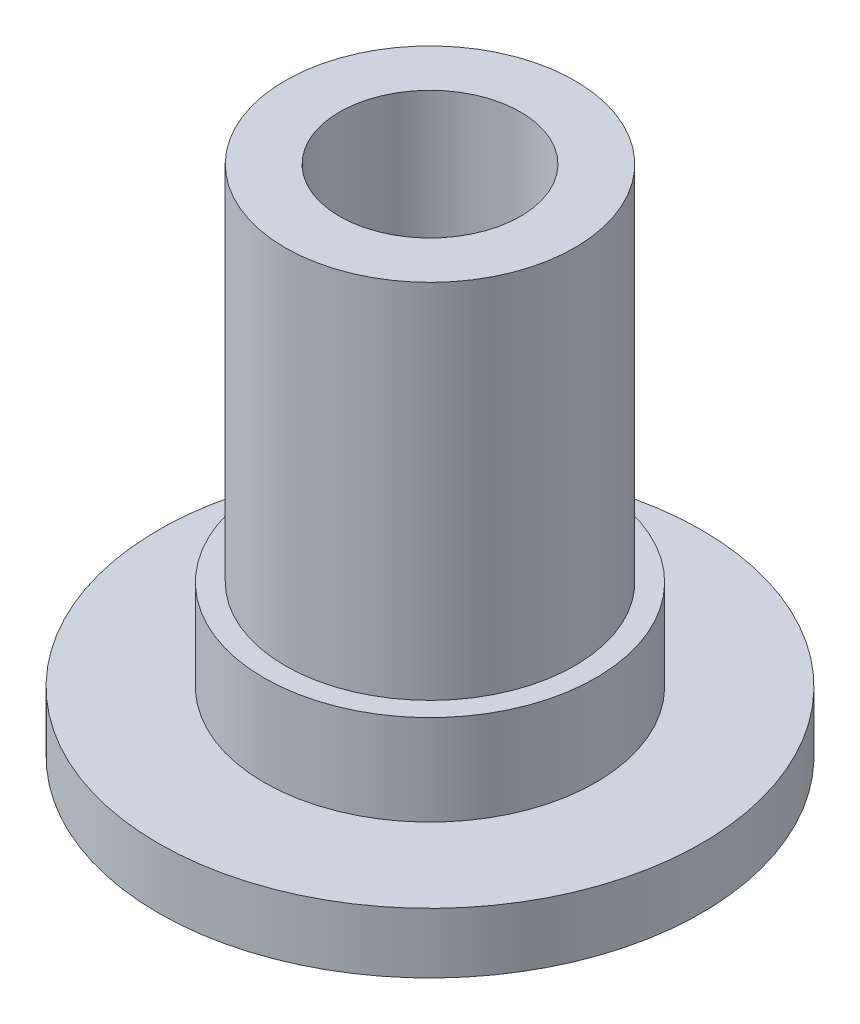
SolidWorks part; units mm, degrees
ref_plane "Спереди" through (0, 0, 0) normal (0, 0, 1) x (1, 0, 0)
ref_plane "Сверху" through (0, 0, 0) normal (0, 1, 0) x (1, 0, 0)
ref_plane "Справа" through (0, 0, 0) normal (1, 0, 0) x (0, 0, -1)
sketch "Эскиз1" plane through (0, 0, 0) normal (0, 1, 0) x (1, 0, 0)
  circle A0 centre (0, 0) radius 9
extrude "Бобышка-Вытянуть1" add sketch "Эскиз1" along normal blind 2
sketch "Эскиз2" plane through (0, 2, 0) normal (0, 1, 0) x (1, 0, 0)
  circle A0 centre (0, 0) radius 5.5
extrude "Бобышка-Вытянуть2" add sketch "Эскиз2" along normal blind 3
sketch "Эскиз5" plane through (0, 5, 0) normal (0, 1, 0) x (1, 0, 0)
  circle A0 centre (0, 0) radius 4.8
extrude "Бобышка-Вытянуть4" add sketch "Эскиз5" along normal blind 12
sketch "Эскиз6" plane through (0, 17, 0) normal (0, 1, 0) x (1, 0, 0)
  circle A0 centre (0, 0) radius 3
extrude "Вырез-Вытянуть2" cut sketch "Эскиз6" against normal through all
